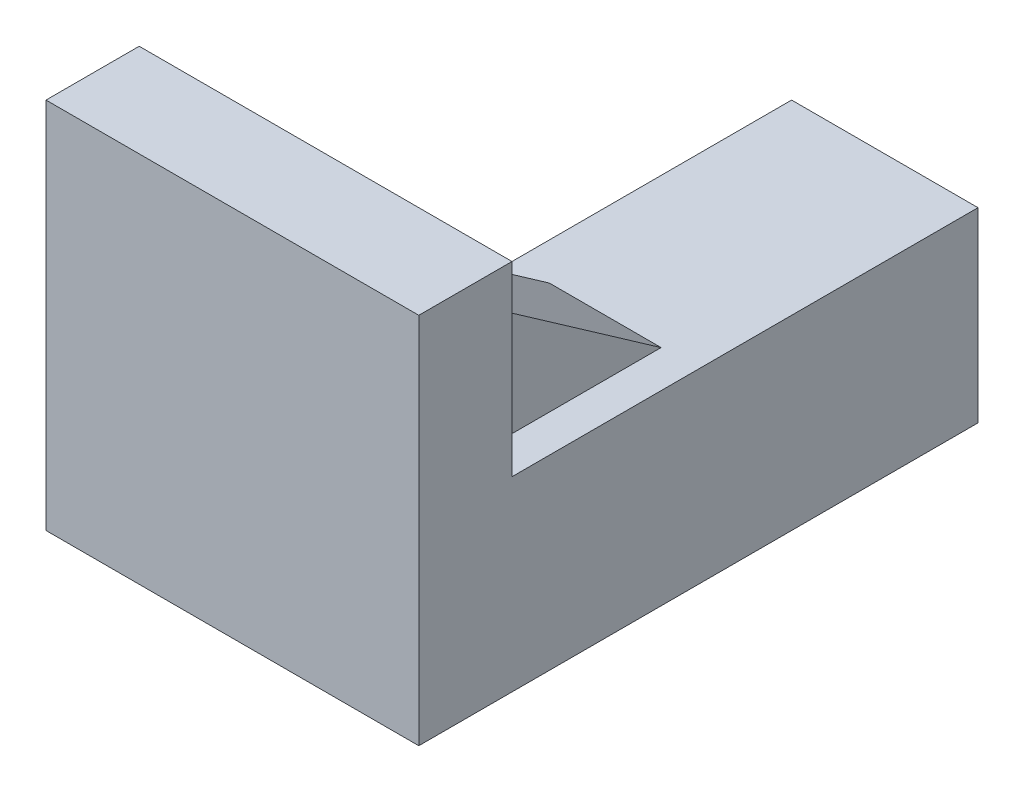
SolidWorks part; units mm, degrees
ref_plane "前视基准面" through (0, 0, 0) normal (0, 0, 1) x (1, 0, 0)
ref_plane "上视基准面" through (0, 0, 0) normal (0, 1, 0) x (1, 0, 0)
ref_plane "右视基准面" through (0, 0, 0) normal (1, 0, 0) x (0, 0, -1)
sketch "草图1" plane through (0, 0, 0) normal (0, 0, 1) x (1, 0, 0)
  line L1 (0, 0) -> (10, 0)
  line L2 (0, 0) -> (0, 10)
  line L3 (0, 10) -> (10, 10)
  line L4 (10, 0) -> (10, 10)
extrude "凸台-拉伸1" add sketch "草图1" along normal blind 25
sketch "草图2" plane through (0, 0, 0) normal (0, 0, -1) x (-1, 0, 0)
  circle A1 centre (-5.7071, 4.2929) radius 1.5
extrude "切除-拉伸1" cut sketch "草图2" against normal blind 15
sketch "草图3" plane through (0, 0, 25) normal (0, 0, 1) x (1, 0, 0)
  line L1 (10, 0) -> (-10, 0)
  line L2 (10, 0) -> (10, 20)
  line L3 (10, 20) -> (-10, 20)
  line L4 (-10, 0) -> (-10, 20)
extrude "凸台-拉伸2" add sketch "草图3" along normal blind 5
sketch "草图4" plane through (0, 0, 25) normal (0, 0, -1) x (-1, 0, 0)
  line L0 (0, 0) -> (0, 10)
  line L1 (0, 5) -> (7, 5)
  line L2 (0, 10) -> (-10, 10)
  line L3 (-10, 10) -> (-5, 10)
  line L4 (-5, 10) -> (-5, 17)
  line L5 (-5, 17) -> (-8, 17)
  line L6 (-8, 17) -> (-5, 17)
  line L7 (-5, 17) -> (-2, 17)
  line L8 (-2, 17) -> (-2, 10)
  line L9 (-8, 17) -> (-8, 10)
  line L10 (7, 5) -> (7, 8)
  line L11 (7, 8) -> (0, 8)
  line L12 (7, 5) -> (7, 2)
  line L13 (7, 2) -> (0, 2)
extrude "凸台-拉伸3" add sketch "草图4" along normal blind 10 contours L10 L11 L0 L1 | L13 L12 L1 L0 | L8 L7 L4 L2 | L5 L9 L3 L4
sketch "草图5" plane through (0, 8, 0) normal (0, 1, 0) x (1, 0, 0)
  line L0 (-7, -25) -> (0, -15)
  line L1 (-7, -15) -> (-7, -25) construction
  line L2 (0, -15) -> (-7, -15)
  line L3 (-7, -15) -> (-7, -25)
extrude "切除-拉伸2" cut sketch "草图5" against normal blind 10
sketch "草图6" plane through (2, 0, 0) normal (-1, 0, 0) x (0, 0, 1)
  line L0 (15, 10) -> (25, 17)
  line L1 (15, 17) -> (15, 10) construction
  line L2 (15, 17) -> (25, 17) construction
  line L3 (25, 17) -> (15, 17)
  line L4 (15, 17) -> (15, 10)
extrude "切除-拉伸3" cut sketch "草图6" against normal blind 10
